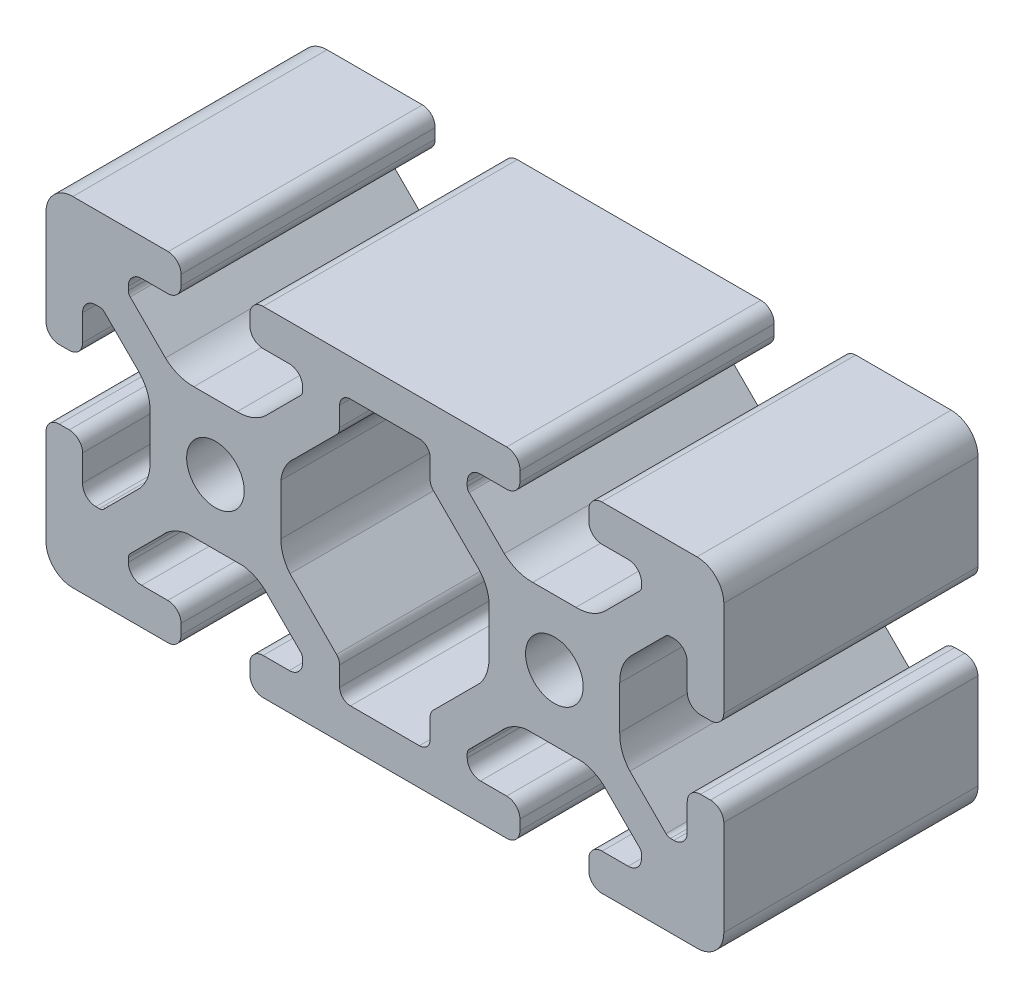
SolidWorks part; units mm, degrees
material "6061 Alloy"
ref_plane "Front Plane" through (0, 0, 0) normal (0, 0, 1) x (1, 0, 0)
ref_plane "Top Plane" through (0, 0, 0) normal (0, 1, 0) x (1, 0, 0)
ref_plane "Right Plane" through (0, 0, 0) normal (1, 0, 0) x (0, 0, -1)
sketch "Sketch1" plane through (0, 0, 0) normal (0, 0, 1) x (1, 0, 0)
  line L0 (-14.3719, 20) -> (14.3719, 20)
  line L1 (-15.94, 17.1729) -> (-15.94, 18.3529)
  line L2 (-11.285, 15.68) -> (-14.37, 15.68)
  line L3 (-9.715, 13.6545) -> (-9.715, 14.11)
  line L4 (4.0718, 15.68) -> (-4.0718, 15.68)
  line L5 (-5.3418, 14.41) -> (-5.3418, 12.1296)
  line L6 (-5.7137, 11.2316) -> (-10.5988, 6.3465)
  line L7 (-12.2841, 3.2591) -> (-12.2841, -2.725)
  line L8 (5.991, -20) -> (-1.7801, -20)
  line L9 (0, 20) -> (0, -25.1394) construction
  line L10 (-4.0718, -15.68) -> (4.0718, -15.68)
  line L11 (-5.3418, -12.1296) -> (-5.3418, -14.41)
  line L12 (-11.2012, -5.7441) -> (-5.7137, -11.2316)
  line L13 (-42.275, 0) -> (43.1806, 0) construction
  line L14 (-9.9376, 13.1171) -> (-14.0919, 8.9628)
  line L15 (-17.4506, 7.7) -> (-22.5494, 7.7)
  line L16 (-25.9081, 8.9628) -> (-30.0624, 13.1171)
  line L17 (-30.285, 13.6545) -> (-30.285, 14.11)
  line L18 (-28.715, 15.68) -> (-25.63, 15.68)
  line L19 (-24.06, 17.25) -> (-24.06, 18.4312)
  line L20 (-25.5696, 20) -> (-33, 20)
  line L21 (-33, 20) -> (-36.83, 20)
  line L22 (-40, 16.8406) -> (-40, 13.0106)
  line L23 (-40, 13.0106) -> (-40, 5.5825)
  line L24 (-38.3243, 4.06) -> (-37.1443, 4.06)
  line L25 (-35.68, 5.6264) -> (-35.68, 8.7114)
  line L26 (-34.11, 10.2814) -> (-33.6509, 10.2814)
  line L27 (-33.1135, 10.0588) -> (-29.0111, 5.9564)
  line L28 (-27.7159, 2.571) -> (-27.7159, -2.502)
  line L29 (-28.9155, -5.8608) -> (-33.1719, -10.1172)
  line L30 (-33.7093, -10.3398) -> (-34.111, -10.3398)
  line L31 (-35.68, -8.715) -> (-35.68, -5.63)
  line L32 (-37.25, -4.06) -> (-38.43, -4.06)
  line L33 (-40, -5.5696) -> (-40, -13)
  line L34 (-40, -13) -> (-40, -16.83)
  line L35 (-37.0574, -20) -> (-33.2274, -20)
  line L36 (-33.2274, -20) -> (-25.797, -20)
  line L37 (-24.06, -18.4389) -> (-24.06, -17.25)
  line L38 (-25.63, -15.68) -> (-28.715, -15.68)
  line L39 (-30.285, -14.11) -> (-30.285, -13.6545)
  line L40 (-30.0624, -13.1171) -> (-26.3095, -9.3642)
  line L41 (-23.3415, -7.7) -> (-16.6585, -7.7)
  line L42 (-13.6905, -9.3642) -> (-9.9376, -13.1171)
  line L43 (-9.715, -13.6545) -> (-9.715, -14.11)
  line L44 (-11.285, -15.68) -> (-14.37, -15.68)
  line L45 (-15.94, -17.25) -> (-15.94, -18.43)
  line L46 (-14.37, -20) -> (-5.991, -20)
  line L47 (-5.991, -20) -> (-1.7801, -20)
  line L48 (14.37, -20) -> (5.991, -20)
  line L49 (15.94, -17.25) -> (15.94, -18.43)
  line L50 (11.285, -15.68) -> (14.37, -15.68)
  line L51 (9.715, -13.6545) -> (9.715, -14.11)
  line L52 (13.6905, -9.3642) -> (9.9376, -13.1171)
  line L53 (23.3415, -7.7) -> (16.6585, -7.7)
  line L54 (30.0624, -13.1171) -> (26.3095, -9.3642)
  line L55 (30.285, -14.11) -> (30.285, -13.6545)
  line L56 (25.63, -15.68) -> (28.715, -15.68)
  line L57 (24.06, -18.4389) -> (24.06, -17.25)
  line L58 (33.2274, -20) -> (25.797, -20)
  line L59 (37.0574, -20) -> (33.2274, -20)
  line L60 (40, -13) -> (40, -16.83)
  line L61 (40, -5.5696) -> (40, -13)
  line L62 (37.25, -4.06) -> (38.43, -4.06)
  line L63 (35.68, -8.715) -> (35.68, -5.63)
  line L64 (33.7093, -10.3398) -> (34.111, -10.3398)
  line L65 (28.9155, -5.8608) -> (33.1719, -10.1172)
  line L66 (27.7159, 2.571) -> (27.7159, -2.502)
  line L67 (33.1135, 10.0588) -> (29.0111, 5.9564)
  line L68 (34.11, 10.2814) -> (33.6509, 10.2814)
  line L69 (35.68, 5.6264) -> (35.68, 8.7114)
  line L70 (38.3243, 4.06) -> (37.1443, 4.06)
  line L71 (40, 13.0106) -> (40, 5.5825)
  line L72 (40, 16.8406) -> (40, 13.0106)
  line L73 (33, 20) -> (36.83, 20)
  line L74 (25.5696, 20) -> (33, 20)
  line L75 (24.06, 17.25) -> (24.06, 18.4312)
  line L76 (28.715, 15.68) -> (25.63, 15.68)
  line L77 (30.285, 13.6545) -> (30.285, 14.11)
  line L78 (25.9081, 8.9628) -> (30.0624, 13.1171)
  line L79 (17.4506, 7.7) -> (22.5494, 7.7)
  line L80 (9.9376, 13.1171) -> (14.0919, 8.9628)
  line L81 (11.2012, -5.7441) -> (5.7137, -11.2316)
  line L82 (5.3418, -12.1296) -> (5.3418, -14.41)
  line L83 (12.2841, 3.2591) -> (12.2841, -2.725)
  line L84 (5.7137, 11.2316) -> (10.5988, 6.3465)
  line L85 (5.3418, 14.41) -> (5.3418, 12.1296)
  line L86 (9.715, 13.6545) -> (9.715, 14.11)
  line L87 (11.285, 15.68) -> (14.37, 15.68)
  line L88 (15.94, 17.1729) -> (15.94, 18.3529)
  line L89 (-20, 24.8708) -> (-20, -18.43) construction
  line L90 (20, 29.4355) -> (20, -23.1087) construction
  line L91 (-3.0962, 16.9038) -> (-43.6857, -23.6857) construction
  line L92 (-36.2671, 16.2671) -> (-2.7875, -17.2125) construction
  arc A0 (-15.94, 18.3529) -> (-14.3719, 20) centre (-14.3719, 18.43) cw
  circle A1 centre (-20, 0) radius 3.4
  arc A2 (-14.37, 15.68) -> (-15.94, 17.1729) centre (-14.3719, 17.25) cw
  arc A3 (-11.285, 15.68) -> (-9.715, 14.11) centre (-11.285, 14.11) cw
  arc A4 (-9.715, 13.6545) -> (-9.9376, 13.1171) centre (-10.475, 13.6545) cw
  arc A5 (-12.2841, -2.725) -> (-11.2012, -5.7441) centre (-7.5341, -2.725) ccw
  arc A6 (-4.0718, 15.68) -> (-5.3418, 14.41) centre (-4.0718, 14.41) ccw
  arc A7 (-5.7137, 11.2316) -> (-5.3418, 12.1296) centre (-6.6118, 12.1296) ccw
  arc A8 (-10.5988, 6.3465) -> (-12.2841, 3.2591) centre (-7.5685, 2.6887) ccw
  arc A9 (-5.3418, -14.41) -> (-4.0718, -15.68) centre (-4.0718, -14.41) ccw
  arc A10 (-5.3418, -12.1296) -> (-5.7137, -11.2316) centre (-6.6118, -12.1296) ccw
  arc A11 (-17.4506, 7.7) -> (-14.0919, 8.9628) centre (-17.3191, 12.4482) ccw
  arc A12 (-25.9081, 8.9628) -> (-22.5494, 7.7) centre (-22.6809, 12.4482) ccw
  arc A13 (-30.285, 13.6545) -> (-30.0624, 13.1171) centre (-29.525, 13.6545) ccw
  arc A14 (-28.715, 15.68) -> (-30.285, 14.11) centre (-28.715, 14.11) ccw
  arc A15 (-25.63, 15.68) -> (-24.06, 17.25) centre (-25.63, 17.25) ccw
  arc A16 (-24.06, 18.4312) -> (-25.5696, 20) centre (-25.63, 18.4312) ccw
  arc A17 (-36.83, 20) -> (-40, 16.8406) centre (-36.83, 16.83) ccw
  arc A18 (-40, 5.5825) -> (-38.3243, 4.06) centre (-38.4306, 5.6264) ccw
  arc A19 (-37.1443, 4.06) -> (-35.68, 5.6264) centre (-37.25, 5.6264) ccw
  arc A20 (-34.11, 10.2814) -> (-35.68, 8.7114) centre (-34.11, 8.7114) ccw
  arc A21 (-33.1135, 10.0588) -> (-33.6509, 10.2814) centre (-33.6509, 9.5214) ccw
  arc A22 (-27.7159, 2.571) -> (-29.0111, 5.9564) centre (-32.4643, 2.6948) ccw
  arc A23 (-28.9155, -5.8608) -> (-27.7159, -2.502) centre (-32.4617, -2.7006) ccw
  arc A24 (-33.7093, -10.3398) -> (-33.1719, -10.1172) centre (-33.7093, -9.5798) ccw
  arc A25 (-35.68, -8.715) -> (-34.111, -10.3398) centre (-34.111, -8.7698) ccw
  arc A26 (-35.68, -5.63) -> (-37.25, -4.06) centre (-37.25, -5.63) ccw
  arc A27 (-38.43, -4.06) -> (-40, -5.5696) centre (-38.4312, -5.63) ccw
  arc A28 (-40, -16.83) -> (-37.0574, -20) centre (-36.83, -16.8382) ccw
  arc A29 (-25.797, -20) -> (-24.06, -18.4389) centre (-25.63, -18.4389) ccw
  arc A30 (-24.06, -17.25) -> (-25.63, -15.68) centre (-25.63, -17.25) ccw
  arc A31 (-30.285, -14.11) -> (-28.715, -15.68) centre (-28.715, -14.11) ccw
  arc A32 (-30.0624, -13.1171) -> (-30.285, -13.6545) centre (-29.525, -13.6545) ccw
  arc A33 (-23.3415, -7.7) -> (-26.3095, -9.3642) centre (-22.6565, -12.4003) ccw
  arc A34 (-13.6905, -9.3642) -> (-16.6585, -7.7) centre (-17.3435, -12.4003) ccw
  arc A35 (-9.715, -13.6545) -> (-9.9376, -13.1171) centre (-10.475, -13.6545) ccw
  arc A36 (-11.285, -15.68) -> (-9.715, -14.11) centre (-11.285, -14.11) ccw
  arc A37 (-14.37, -15.68) -> (-15.94, -17.25) centre (-14.37, -17.25) ccw
  arc A38 (-15.94, -18.43) -> (-14.37, -20) centre (-14.37, -18.43) ccw
  arc A39 (15.94, -18.43) -> (14.37, -20) centre (14.37, -18.43) cw
  arc A40 (14.37, -15.68) -> (15.94, -17.25) centre (14.37, -17.25) cw
  arc A41 (11.285, -15.68) -> (9.715, -14.11) centre (11.285, -14.11) cw
  arc A42 (9.715, -13.6545) -> (9.9376, -13.1171) centre (10.475, -13.6545) cw
  arc A43 (13.6905, -9.3642) -> (16.6585, -7.7) centre (17.3435, -12.4003) cw
  arc A44 (23.3415, -7.7) -> (26.3095, -9.3642) centre (22.6565, -12.4003) cw
  arc A45 (30.0624, -13.1171) -> (30.285, -13.6545) centre (29.525, -13.6545) cw
  arc A46 (30.285, -14.11) -> (28.715, -15.68) centre (28.715, -14.11) cw
  arc A47 (24.06, -17.25) -> (25.63, -15.68) centre (25.63, -17.25) cw
  arc A48 (25.797, -20) -> (24.06, -18.4389) centre (25.63, -18.4389) cw
  arc A49 (40, -16.83) -> (37.0574, -20) centre (36.83, -16.8382) cw
  arc A50 (38.43, -4.06) -> (40, -5.5696) centre (38.4312, -5.63) cw
  arc A51 (35.68, -5.63) -> (37.25, -4.06) centre (37.25, -5.63) cw
  arc A52 (35.68, -8.715) -> (34.111, -10.3398) centre (34.111, -8.7698) cw
  arc A53 (33.7093, -10.3398) -> (33.1719, -10.1172) centre (33.7093, -9.5798) cw
  arc A54 (28.9155, -5.8608) -> (27.7159, -2.502) centre (32.4617, -2.7006) cw
  arc A55 (27.7159, 2.571) -> (29.0111, 5.9564) centre (32.4643, 2.6948) cw
  arc A56 (33.1135, 10.0588) -> (33.6509, 10.2814) centre (33.6509, 9.5214) cw
  arc A57 (34.11, 10.2814) -> (35.68, 8.7114) centre (34.11, 8.7114) cw
  arc A58 (37.1443, 4.06) -> (35.68, 5.6264) centre (37.25, 5.6264) cw
  arc A59 (40, 5.5825) -> (38.3243, 4.06) centre (38.4306, 5.6264) cw
  arc A60 (36.83, 20) -> (40, 16.8406) centre (36.83, 16.83) cw
  arc A61 (24.06, 18.4312) -> (25.5696, 20) centre (25.63, 18.4312) cw
  arc A62 (25.63, 15.68) -> (24.06, 17.25) centre (25.63, 17.25) cw
  arc A63 (28.715, 15.68) -> (30.285, 14.11) centre (28.715, 14.11) cw
  arc A64 (30.285, 13.6545) -> (30.0624, 13.1171) centre (29.525, 13.6545) cw
  arc A65 (25.9081, 8.9628) -> (22.5494, 7.7) centre (22.6809, 12.4482) cw
  arc A66 (17.4506, 7.7) -> (14.0919, 8.9628) centre (17.3191, 12.4482) cw
  arc A67 (5.3418, -12.1296) -> (5.7137, -11.2316) centre (6.6118, -12.1296) cw
  arc A68 (5.3418, -14.41) -> (4.0718, -15.68) centre (4.0718, -14.41) cw
  arc A69 (10.5988, 6.3465) -> (12.2841, 3.2591) centre (7.5685, 2.6887) cw
  arc A70 (5.7137, 11.2316) -> (5.3418, 12.1296) centre (6.6118, 12.1296) cw
  arc A71 (4.0718, 15.68) -> (5.3418, 14.41) centre (4.0718, 14.41) cw
  arc A72 (12.2841, -2.725) -> (11.2012, -5.7441) centre (7.5341, -2.725) cw
  arc A73 (9.715, 13.6545) -> (9.9376, 13.1171) centre (10.475, 13.6545) ccw
  arc A74 (11.285, 15.68) -> (9.715, 14.11) centre (11.285, 14.11) ccw
  arc A75 (14.37, 15.68) -> (15.94, 17.1729) centre (14.3719, 17.25) ccw
  circle A76 centre (20, 0) radius 3.4
  arc A77 (15.94, 18.3529) -> (14.3719, 20) centre (14.3719, 18.43) ccw
  dimension "D4" = 6.8
  dimension "D1" = 80
  dimension "D2" = 40
  dimension "D3" = 20
  dimension "D5" = 8.12
  dimension "D6" = 4.32
  dimension "D7" = 20.57
  dimension "D8" = 4.32
  dimension "D9" = 8.12
  dimension "D10" = 12.3
  dimension "D11" = 4.32
  dimension "D12" = 4.32
  dimension "D13" = 4.32
extrude "Extrude1" add sketch "Sketch1" against normal blind 30
